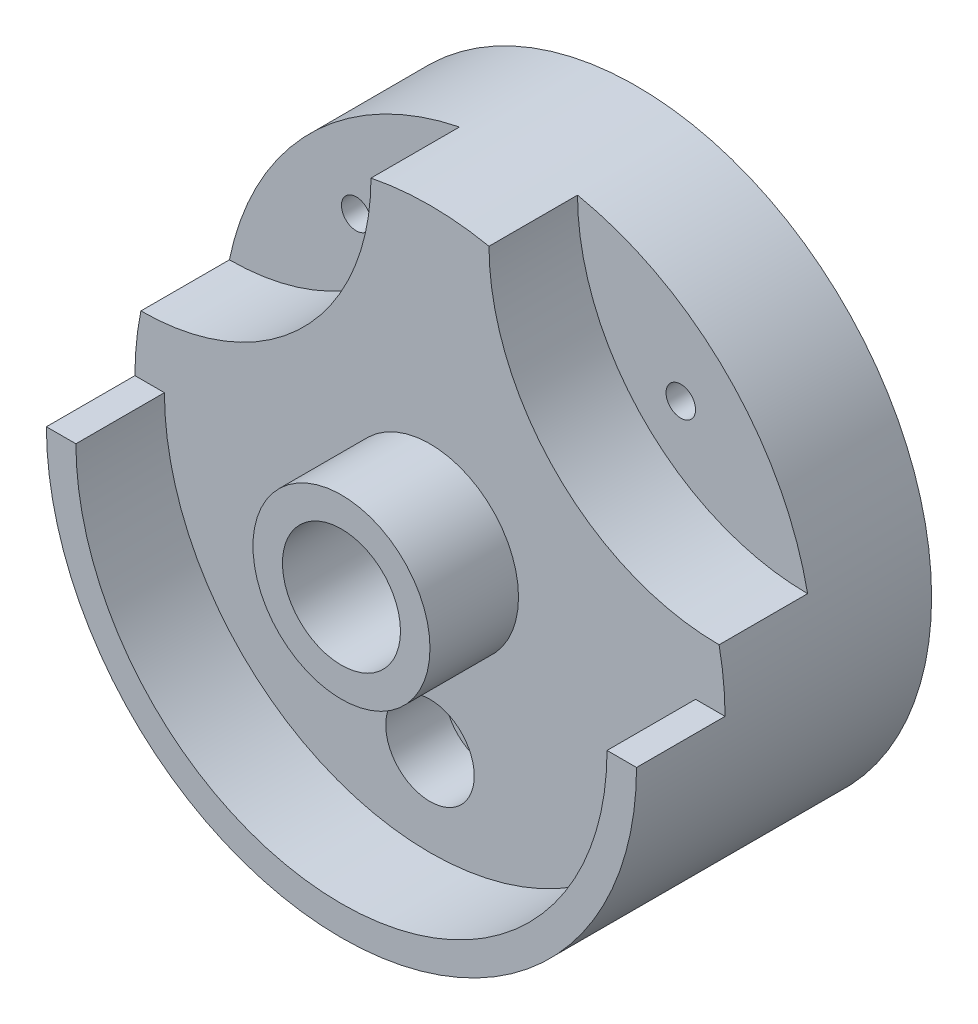
SolidWorks part; units mm, degrees
ref_plane "Front Plane" through (0, 0, 0) normal (0, 0, 1) x (1, 0, 0)
ref_plane "Top Plane" through (0, 0, 0) normal (0, 1, 0) x (1, 0, 0)
ref_plane "Right Plane" through (0, 0, 0) normal (1, 0, 0) x (0, 0, -1)
sketch "Sketch1" plane through (0, 0, 0) normal (0, 0, 1) x (1, 0, 0)
  circle A0 centre (0, 0) radius 50
  dimension "D1" = 100
extrude "Boss-Extrude1" add sketch "Sketch1" along normal blind 20
sketch "Sketch2" plane through (0, 0, 20) normal (0, 0, 1) x (1, 0, 0)
  line L0 (-50, 0) -> (-45, 0)
  line L1 (45, 0) -> (50, 0)
  circle A0 centre (0, 0) radius 50 construction
  arc A1 (-45, 0) -> (45, 0) centre (0, 0) ccw
  arc A2 (-50, 0) -> (50, 0) centre (0, 0) ccw
  dimension "D3" = 45
  dimension "D4" = 50
  dimension "D1" = 5
  dimension "D2" = 5
extrude "Boss-Extrude3" add sketch "Sketch2" along normal blind 30
sketch "Sketch4" plane through (0, 0, 20) normal (0, 0, 1) x (1, 0, 0)
  line L0 (-50, 0) -> (-45, 0)
  line L1 (45, 0) -> (50, 0)
  arc A0 (-48.9898, 10) -> (-10, 48.9898) centre (-48.9898, 48.9898) ccw
  arc A1 (-48.9898, 10) -> (-10, 48.9898) centre (0, 0) cw
  arc A2 (50, 0) -> (-50, 0) centre (0, 0) ccw construction
  arc A3 (10, 48.9898) -> (48.9898, 10) centre (48.9898, 48.9898) ccw
  arc A4 (48.9898, 10) -> (10, 48.9898) centre (0, 0) ccw
  arc A5 (-48.9898, 10) -> (-50, 0) centre (0, 0) ccw
  arc A6 (-45, 0) -> (45, 0) centre (0, 0) ccw construction
  arc A7 (-45, 0) -> (45, 0) centre (0, 0) ccw
  arc A8 (50, 0) -> (48.9898, 10) centre (0, 0) ccw
  dimension "D3" = 50
  dimension "D2" = 50
  dimension "D1" = 10
extrude "Boss-Extrude7" add sketch "Sketch4" along normal blind 15
sketch "Sketch5" plane through (0, 0, 20) normal (0, 0, 1) x (1, 0, 0)
  circle A0 centre (-27.5, 27.5) radius 2.5
  circle A1 centre (27.5, 27.5) radius 2.5
  dimension "D5" = 5
  dimension "D6" = 5
  dimension "D1" = 27.5
  dimension "D2" = 27.5
  dimension "D3" = 27.5
  dimension "D4" = 27.5
extrude "Cut-Extrude1" cut sketch "Sketch5" against normal blind 43
sketch "Sketch8" plane through (0, 0, 35) normal (0, 0, 1) x (1, 0, 0)
  circle A0 centre (0, -30) radius 7.5
  dimension "D1" = 15
  dimension "D3" = 45
  dimension "D2" = 30
extrude "Cut-Extrude4" cut sketch "Sketch8" against normal blind 10
sketch "Sketch9" plane through (0, 0, 25) normal (0, 0, 1) x (1, 0, 0)
  circle A0 centre (0, -30) radius 2.5
  dimension "D1" = 5
extrude "Cut-Extrude5" cut sketch "Sketch9" against normal blind 90
sketch "Sketch10" plane through (0, 0, 0) normal (0, 0, -1) x (-1, 0, 0)
  circle A0 centre (0, -30) radius 12.5
extrude "Cut-Extrude6" cut sketch "Sketch10" against normal blind 10
sketch "Sketch11" plane through (0, 0, 35) normal (0, 0, 1) x (1, 0, 0)
  circle A0 centre (0, 0) radius 15
extrude "Boss-Extrude8" add sketch "Sketch11" along normal blind 15
sketch "Sketch12" plane through (0, 0, 50) normal (0, 0, 1) x (1, 0, 0)
  circle A0 centre (0, 0) radius 10
extrude "Cut-Extrude7" cut sketch "Sketch12" against normal blind 105
